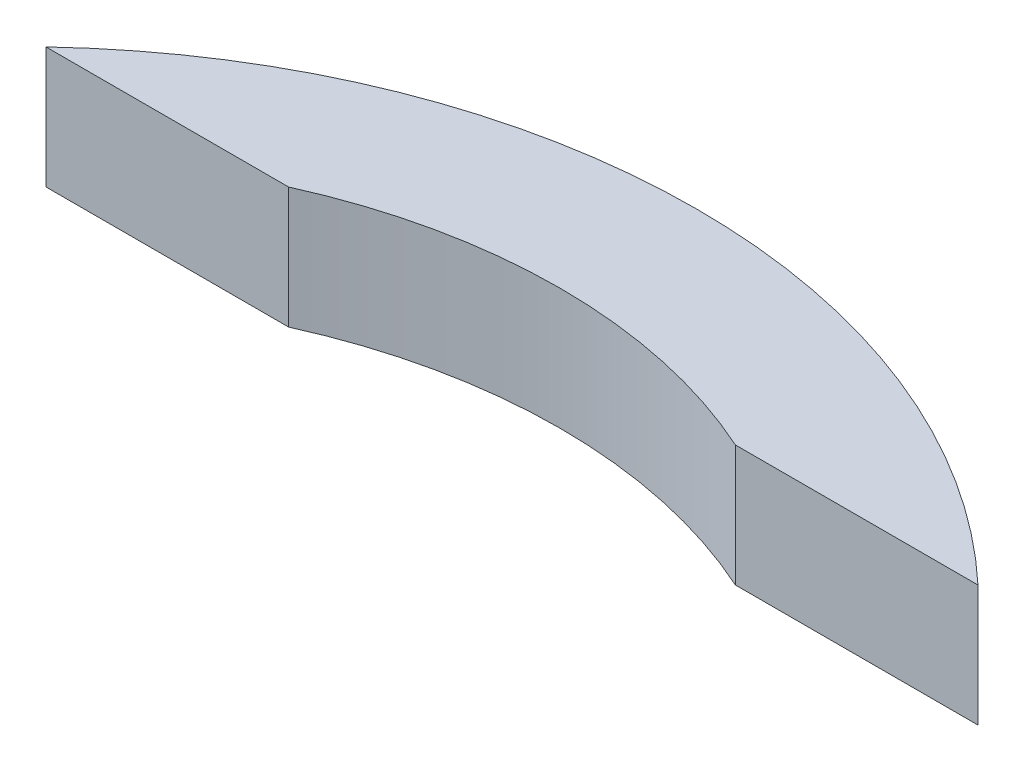
SolidWorks part; units mm, degrees
material "1.0035 (S185)"
ref_plane "Front Plane" through (0, 0, 0) normal (0, 0, 1) x (1, 0, 0)
ref_plane "Top Plane" through (0, 0, 0) normal (0, 1, 0) x (1, 0, 0)
ref_plane "Right Plane" through (0, 0, 0) normal (1, 0, 0) x (0, 0, -1)
sketch "Sketch4" plane through (0, 0, 0) normal (0, 0, 1) x (1, 0, 0)
  line L32 (0, 40.5) -> (0, -40.5)
  line L33 (0, -40.5) -> (162, -40.5)
  line L34 (162, -40.5) -> (162, 40.5)
  line L35 (162, 40.5) -> (0, 40.5)
  line L36 (81, -58.943) -> (81, 56.7242) construction
  point P2 (162, 0)
  point P5 (0, 0)
  point P10 (81, 40.5)
  dimension "D1" = 81
  dimension "D2" = 162
sketch "Sketch1" plane through (0, 0, 0) normal (0, 0, 1) x (1, 0, 0)
  line L46 (71.5, 130) -> (-3.5, 130)
  line L47 (-3.5, 130) -> (-3.5, -130)
  line L48 (-3.5, -130) -> (71.5, -130)
  line L49 (71.5, -130) -> (71.5, -118)
  line L50 (71.5, -118) -> (15.5, -118)
  line L51 (3.5, -106) -> (3.5, 106)
  line L52 (15.5, 118) -> (71.5, 118)
  line L53 (71.5, 118) -> (71.5, 130)
  arc A4 (3.5, 106) -> (15.5, 118) centre (15.5, 106) cw
  arc A5 (15.5, -118) -> (3.5, -106) centre (15.5, -106) cw
  dimension "D6" = 12
  dimension "D1" = 75
  dimension "D2" = 260
  dimension "D3" = 7
  dimension "D4" = 12
  dimension "D5" = 12
  dimension "D7" = 3.5
  dimension "D8" = 130
sketch3d "3DSketch1"
  line L0 (0, 0, 0) -> (622.3, 0, 0) construction
  line L2 (0, 0, 0) -> (197.7581, 0, -186.3578) construction
  line L3 (622.3, 0, 0) -> (428.6902, 0, -182.4487) construction
  arc A2 (0, 0, 0) -> (744.1778, 0, 194.8222) centre (311.15, 0, 330.1844) cw
  point P6 (311.15, 0, 0)
  point P11 (311.15, -453.6916, 330.1844)
  point P12 (436.4176, 0, 366.1978)
  dimension "D1" = 43.3
  dimension "D2" = 43.3
  dimension "D3" = 622.3
sweep "Sweep1" add profiles "Sketch4" path "3DSketch1"
sketch "Sketch3" plane through (0, 0, 0) normal (0, 0, 1) x (1, 0, 0)
  line L1 (-246.3461, 991.572) -> (1079.0289, 991.572)
  line L2 (-246.3461, 991.572) -> (-246.3461, -997.5447)
  line L3 (-246.3461, -997.5447) -> (1079.0289, -997.5447)
  line L4 (1079.0289, 991.572) -> (1079.0289, -997.5447)
extrude "Cut-Extrude1" cut sketch "Sketch3" along normal through all
sketch "Sketch5" plane through (0, -40.5, 0) normal (0, -1, 0) x (1, 0, 0)
  line L0 (0, 0) -> (162, 0) construction
  line L1 (147, 0) -> (262, 0)
  line L2 (147, 0) -> (147, -20)
  line L3 (147, -20) -> (262, -20)
  line L4 (262, 0) -> (262, -20)
  dimension "D1" = 15
  dimension "D2" = 100
  dimension "br_DS" = 20
extrude "Cut-Extrude2" [suppressed] cut sketch "Sketch5" against normal through all
sketch "Sketch6" plane through (0, 0, 0) normal (0, 0, 1) x (1, 0, 0)
  line L12 (0, 56) -> (0, -56)
  line L17 (0, -56) -> (10.2, -56)
  line L18 (10.2, -56) -> (10.2, -19.3)
  line L23 (26.2, -3.3) -> (195.8, -3.3)
  line L24 (211.8, -19.3) -> (211.8, -56)
  line L25 (211.8, -56) -> (222, -56)
  line L26 (222, -56) -> (222, 56)
  line L27 (222, 56) -> (211.8, 56)
  line L28 (211.8, 56) -> (211.8, 19.3)
  line L29 (195.8, 3.3) -> (26.2, 3.3)
  line L30 (10.2, 19.3) -> (10.2, 56)
  line L31 (10.2, 56) -> (0, 56)
  arc A0 (10.2, -19.3) -> (26.2, -3.3) centre (26.2, -19.3) cw
  arc A1 (26.2, 3.3) -> (10.2, 19.3) centre (26.2, 19.3) cw
  arc A2 (195.8, 3.3) -> (211.8, 19.3) centre (195.8, 19.3) ccw
  arc A3 (195.8, -3.3) -> (211.8, -19.3) centre (195.8, -19.3) cw
  point P2 (111, 3.3)
  point P13 (111, -3.3)
  dimension "D8" = 16
  dimension "D1" = 222
  dimension "D2" = 112
  dimension "D3" = 6.6
  dimension "D4" = 10.2
  dimension "D5" = 10.2
equation "\"D5@Sketch1\"=\"D4@Sketch1\""
equation "\"D7@Sketch1\"=\"D3@Sketch1\"/2"
equation "\"D8@Sketch1\"=\"D2@Sketch1\"/2"
